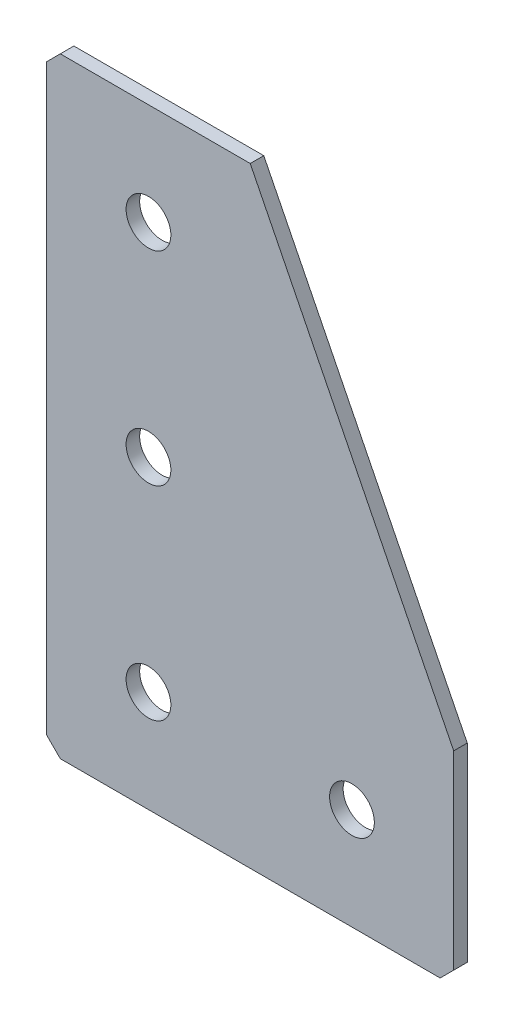
SolidWorks part; units mm, degrees
material "Простая углеродистая сталь"
ref_plane "Спереди(Плоскость XY)" through (0, 0, 0) normal (0, 0, 1) x (1, 0, 0)
ref_plane "Сверху(Плоскость XZ)" through (0, 0, 0) normal (0, 1, 0) x (1, 0, 0)
ref_plane "Справа(Плоскость ZY)" through (0, 0, 0) normal (1, 0, 0) x (0, 0, -1)
sketch "Эскиз1" plane through (0, 0, 0) normal (0, 0, -1) x (1, 0, 0)
  line L0 (0, 0) -> (0, 90)
  line L1 (0, 90) -> (60, 90)
  line L2 (60, 90) -> (60, 60)
  line L3 (60, 60) -> (30, 60) construction
  line L4 (30, 60) -> (30, 0) construction
  line L5 (30, 0) -> (0, 0)
  line L6 (60, 60) -> (30, 0)
  dimension "D1" = 90
  dimension "D2" = 30
  dimension "D3" = 30
  dimension "D4" = 30
extrude "Бобышка-Вытянуть1" add sketch "Эскиз1" along normal blind 2
hole_wizard "Отверстие с зазором M61" positions "Эскиз2" profile "Эскиз3" hole size "M6" standard "DIN" end condition through all
sketch "Эскиз2" plane through (0, 0, -2) normal (0, 0, -1) x (1, 0, 0)
  line L1 (0, 0) -> (30, 0) construction
  line L6 (0, 90) -> (0, 0) construction
  point P0 (45, 75)
  point P2 (15, 75)
  point P4 (15, 45)
  point P6 (15, 15)
  dimension "D1" = 30
  dimension "D2" = 30
  dimension "D3" = 30
  dimension "D4" = 15
  dimension "D5" = 15
sketch "Эскиз3" plane through (45, -75, -2) normal (1, 0, 0) x (0, 1, 0)
  line L0 (0, 0) -> (0, 2)
  line L1 (0, 2) -> (3.3, 2)
  line L2 (3.3, 2) -> (3.3, 0)
  line L5 (3.3, 0) -> (0, 0)
  line L11 (0, -6.35) -> (0, 107.95) construction
  dimension "Диаметр сквозного отверстия" = 6.6
  dimension "Глубина сквозного отверстия" = 2
chamfer "Фаска1" distance 2 angle 45 3 edges at (0, 0, -1) (60, -90, -1) (0, -90, -1)
